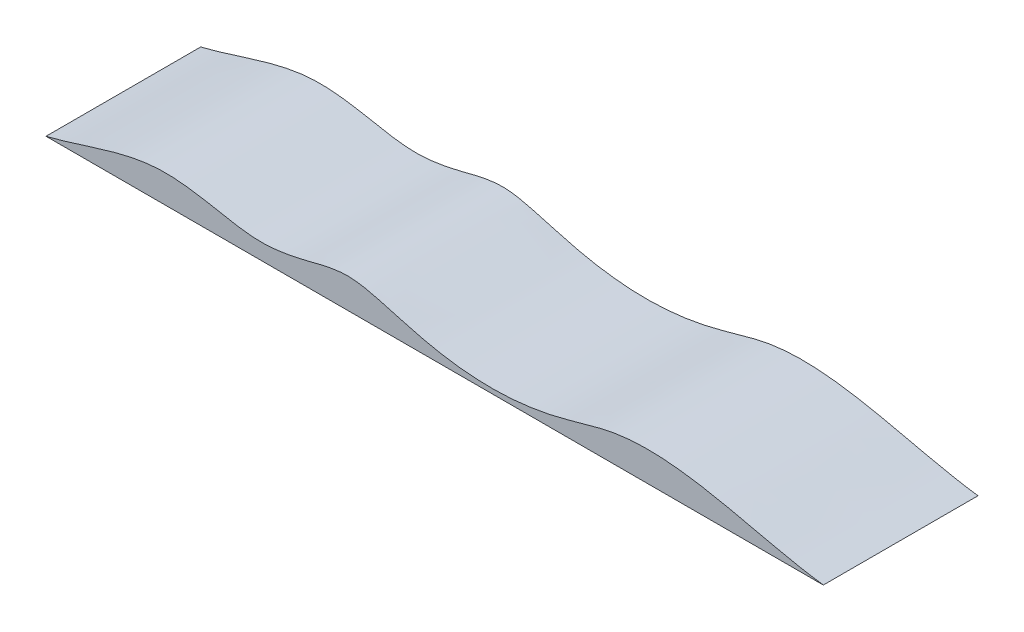
SolidWorks part; units mm, degrees
material "红木"
ref_plane "前视基准面" through (0, 0, 0) normal (0, 0, 1) x (1, 0, 0)
ref_plane "上视基准面" through (0, 0, 0) normal (0, 1, 0) x (1, 0, 0)
ref_plane "右视基准面" through (0, 0, 0) normal (1, 0, 0) x (0, 0, -1)
other "Configuration Table"
sketch "草图1" plane through (0, 0, 0) normal (0, 0, 1) x (1, 0, 0)
  line L0 (-275.2782, -25.783) -> (981.0488, -25.783)
  spline S0 degree 3 poles (-275.2782, -25.783) (-214.8422, -11.3044) (-126.4372, 29.8526) (-8.9897, 12.2788) (68.9854, -5.3427) (143.445, 8.8105) (206.9347, 27.7153) (270.5432, 12.9797) (345.3034, -10.1417) (444.0991, -23.0301) (548.2562, -9.5903) (721.2127, 50.3804) (872.0265, -11.2659) (981.0488, -25.783) knots 0 0 0 0 0.150156 0.213516 0.27628 0.335934 0.389672 0.428666 0.486345 0.57479 0.659788 0.731421 1 1 1 1
  point P2 (0, 0)
  point P3 (0, 0)
  point P4 (0, 0)
  point P6 (0, 0)
  point P7 (0, 0)
  point P8 (0, 0)
  point P10 (0, 0)
  point P12 (0, 0)
  point P14 (0, 0)
  point P16 (0, 0)
  point P18 (0, 0)
  point P20 (0, 0)
  point P22 (0, 0)
  point P24 (0, 0)
  point P26 (0, 0)
  point P28 (0, 0)
  point P30 (0, 0)
  point P31 (0, 0)
  point P32 (0, 0)
  point P33 (0, 0)
  point P34 (0, 0)
  point P35 (0, 0)
extrude "凸台-拉伸2" add sketch "草图1" along normal mid plane 250 contours S0 L0
